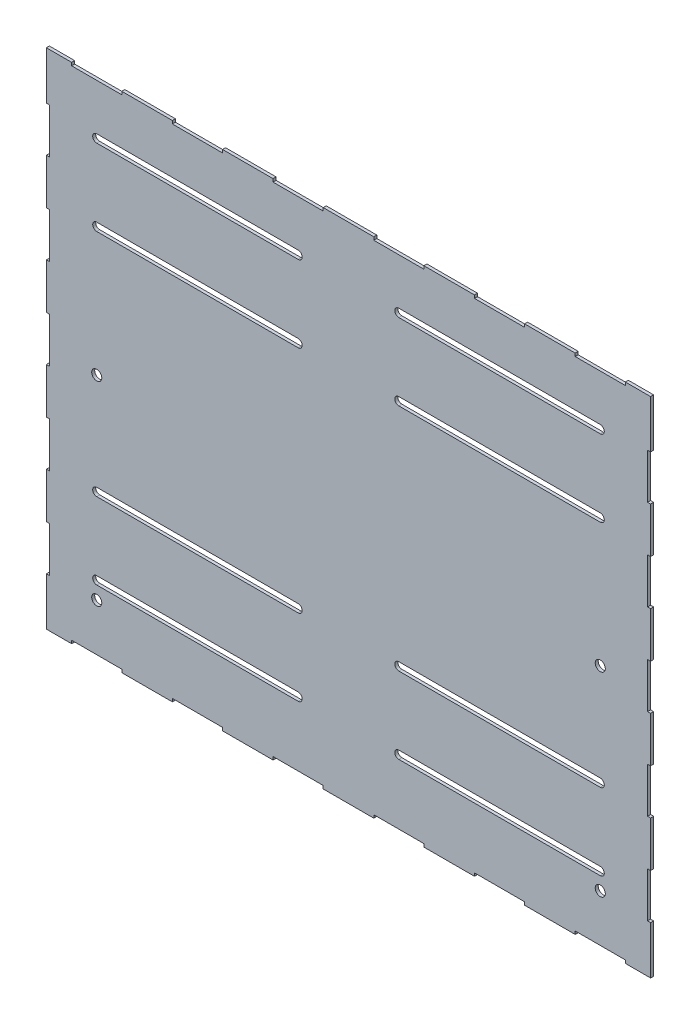
SolidWorks part; units mm, degrees
ref_plane "Alzado" through (0, 0, 0) normal (0, 0, 1) x (1, 0, 0)
ref_plane "Planta" through (0, 0, 0) normal (0, 1, 0) x (1, 0, 0)
ref_plane "Vista lateral" through (0, 0, 0) normal (1, 0, 0) x (0, 0, -1)
sketch "Croquis1" plane through (0, 0, 0) normal (0, 0, 1) x (1, 0, 0)
  line L0 (-250, 197) -> (-50, 197) construction
  line L1 (-300, 250) -> (300, 250)
  line L2 (-300, 250) -> (-300, -250)
  line L3 (-300, -250) -> (300, -250)
  line L4 (300, 250) -> (300, -250)
  line L5 (-300, 250) -> (300, -250) construction
  line L6 (-300, -250) -> (300, 250) construction
  line L7 (-250, 201) -> (-50, 201)
  line L8 (-250, 193) -> (-50, 193)
  line L9 (-250, 117) -> (-50, 117)
  line L10 (-250, 125) -> (-50, 125)
  line L11 (-250, 121) -> (-50, 121) construction
  line L20 (0, 250) -> (0, 163.6039) construction
  line L25 (250, -107) -> (50, -107) construction
  line L26 (-250, -111) -> (-50, -111)
  line L27 (-250, -103) -> (-50, -103)
  line L28 (-250, -107) -> (-50, -107) construction
  line L29 (-250, -187) -> (-50, -187)
  line L30 (-250, -179) -> (-50, -179)
  line L31 (-250, -183) -> (-50, -183) construction
  line L32 (-250, 49) -> (-50, 49) [skipped]
  line L33 (-250, 41) -> (-50, 41) [skipped]
  line L34 (-250, -27) -> (-50, -27) [skipped]
  line L35 (-250, -35) -> (-50, -35) [skipped]
  line L36 (250, -103) -> (50, -103)
  line L37 (250, -111) -> (50, -111)
  line L38 (250, -183) -> (50, -183) construction
  line L39 (250, -179) -> (50, -179)
  line L40 (250, -187) -> (50, -187)
  line L41 (250, 197) -> (50, 197) construction
  line L42 (250, 201) -> (50, 201)
  line L43 (250, 193) -> (50, 193)
  line L44 (250, 121) -> (50, 121) construction
  line L45 (250, 125) -> (50, 125)
  line L46 (250, 117) -> (50, 117)
  line L47 (-241.3, 43.5) -> (241.3, 43.5) construction
  line L48 (0, 0) -> (0, -70.2639) construction
  arc A0 (-250, 201) -> (-250, 193) centre (-250, 197) ccw
  arc A1 (-50, 193) -> (-50, 201) centre (-50, 197) ccw
  arc A10 (-250, 125) -> (-250, 117) centre (-250, 121) ccw
  arc A11 (-50, 117) -> (-50, 125) centre (-50, 121) ccw
  arc A16 (-250, -103) -> (-250, -111) centre (-250, -107) ccw
  arc A17 (-50, -111) -> (-50, -103) centre (-50, -107) ccw
  arc A18 (-250, -179) -> (-250, -187) centre (-250, -183) ccw
  arc A19 (-50, -187) -> (-50, -179) centre (-50, -183) ccw
  arc A20 (-250, 49) -> (-250, 41) centre (-250, 45) ccw [skipped]
  arc A21 (-50, 41) -> (-50, 49) centre (-50, 45) ccw [skipped]
  arc A22 (-250, -27) -> (-250, -35) centre (-250, -31) ccw [skipped]
  arc A23 (-50, -35) -> (-50, -27) centre (-50, -31) ccw [skipped]
  arc A24 (250, -103) -> (250, -111) centre (250, -107) cw
  arc A25 (50, -111) -> (50, -103) centre (50, -107) cw
  arc A26 (250, -179) -> (250, -187) centre (250, -183) cw
  arc A27 (50, -187) -> (50, -179) centre (50, -183) cw
  arc A28 (250, 201) -> (250, 193) centre (250, 197) cw
  arc A29 (50, 193) -> (50, 201) centre (50, 197) cw
  arc A30 (250, 125) -> (250, 117) centre (250, 121) cw
  arc A31 (50, 117) -> (50, 125) centre (50, 121) cw
  circle A32 centre (-250, -200) radius 5
  circle A33 centre (-250, -6.5) radius 5
  circle A34 centre (250, -200) radius 5
  circle A35 centre (250, -6.5) radius 5
  point P0 (0, 0)
  point P8 (-150, 197)
  point P17 (-150, 121)
  point P24 (150, -107)
  point P31 (150, -183)
  point P38 (-150, -107)
  point P45 (-150, -183)
  point P72 (150, 197)
  point P79 (150, 121)
  dimension "D5" = 200
  dimension "D10" = 10
  dimension "D12" = 10
  dimension "D1" = 500
  dimension "D2" = 600
  dimension "D3" = 8
  dimension "D4" = 49
  dimension "D6" = 50
  dimension "D8" = 6
  dimension "D7" = 76
  dimension "D9" = 50
  dimension "D11" = 50
  dimension "D13" = 50
  dimension "D14" = 50
extrude "Saliente-Extruir1" add sketch "Croquis1" along normal blind 3 contours L1 A35 A33 L2 L3 L4 L46 A31 L45 A30 L43 A29 L42 A28 L40 A27 L39 A26 L37 A25 L36 A24 A1 L8 A0 L7 A11 L9 A10 L10 A17 L26 A16 L27 A19 L29 A18 L30 A32
sketch "Croquis5" plane through (0, 0, 0) normal (0, 0, -1) x (-1, 0, 0)
  line L0 (300, 250) -> (-300, 250) construction
  line L1 (300, 250) -> (300, -250) construction
  line L2 (125.1, 250) -> (125.1, 247)
  line L3 (125.1, 247) -> (174.9, 247)
  line L28 (174.9, 247) -> (174.9, 250)
  line L29 (174.9, 250) -> (125.1, 250)
  line L30 (25.1, 250) -> (25.1, 247)
  line L31 (25.1, 247) -> (74.9, 247)
  line L32 (225.1, 250) -> (225.1, 247)
  line L33 (225.1, 247) -> (274.9, 247)
  line L34 (274.9, 247) -> (274.9, 250)
  line L35 (274.9, 250) -> (225.1, 250)
  line L52 (74.9, 247) -> (74.9, 250)
  line L53 (74.9, 250) -> (25.1, 250)
  line L54 (-74.9, 250) -> (-74.9, 247)
  line L55 (-74.9, 247) -> (-25.1, 247)
  line L148 (-25.1, 247) -> (-25.1, 250)
  line L149 (-25.1, 250) -> (-74.9, 250)
  line L150 (-174.9, 250) -> (-174.9, 247)
  line L151 (-174.9, 247) -> (-125.1, 247)
  line L152 (297, 202.4) -> (297, 157.6)
  line L153 (297, 157.6) -> (300, 157.6)
  line L154 (300, 157.6) -> (300, 202.4)
  line L155 (300, 202.4) -> (297, 202.4)
  line L156 (-125.1, 247) -> (-125.1, 250)
  line L157 (-125.1, 250) -> (-174.9, 250)
  line L158 (-274.9, 250) -> (-274.9, 247)
  line L159 (-274.9, 247) -> (-225.1, 247)
  line L160 (-225.1, 247) -> (-225.1, 250)
  line L161 (-225.1, 250) -> (-274.9, 250)
  line L182 (297, 112.4) -> (297, 67.6)
  line L183 (297, 67.6) -> (300, 67.6)
  line L184 (300, 67.6) -> (300, 112.4)
  line L185 (300, 112.4) -> (297, 112.4)
  line L186 (297, 22.4) -> (297, -22.4)
  line L187 (297, -22.4) -> (300, -22.4)
  line L188 (300, -22.4) -> (300, 22.4)
  line L189 (300, 22.4) -> (297, 22.4)
  line L190 (297, -67.6) -> (297, -112.4)
  line L191 (297, -112.4) -> (300, -112.4)
  line L192 (300, -112.4) -> (300, -67.6)
  line L193 (300, -67.6) -> (297, -67.6)
  line L194 (297, -157.6) -> (297, -202.4)
  line L195 (297, -202.4) -> (300, -202.4)
  line L196 (300, -202.4) -> (300, -157.6)
  line L197 (300, -157.6) -> (297, -157.6)
  line L198 (0, 0) -> (0, 89.4251) construction
  line L199 (0, 0) -> (95.335, 0) construction
  line L200 (-225.1, -250) -> (-274.9, -250)
  line L201 (-225.1, -247) -> (-225.1, -250)
  line L202 (-274.9, -247) -> (-225.1, -247)
  line L203 (-274.9, -250) -> (-274.9, -247)
  line L204 (-125.1, -250) -> (-174.9, -250)
  line L205 (-125.1, -247) -> (-125.1, -250)
  line L206 (-174.9, -247) -> (-125.1, -247)
  line L207 (-174.9, -250) -> (-174.9, -247)
  line L208 (-25.1, -250) -> (-74.9, -250)
  line L209 (-25.1, -247) -> (-25.1, -250)
  line L210 (-74.9, -247) -> (-25.1, -247)
  line L211 (-74.9, -250) -> (-74.9, -247)
  line L212 (74.9, -250) -> (25.1, -250)
  line L213 (74.9, -247) -> (74.9, -250)
  line L214 (274.9, -250) -> (225.1, -250)
  line L215 (274.9, -247) -> (274.9, -250)
  line L216 (225.1, -247) -> (274.9, -247)
  line L217 (225.1, -250) -> (225.1, -247)
  line L218 (25.1, -247) -> (74.9, -247)
  line L219 (25.1, -250) -> (25.1, -247)
  line L220 (174.9, -250) -> (125.1, -250)
  line L221 (174.9, -247) -> (174.9, -250)
  line L222 (125.1, -247) -> (174.9, -247)
  line L223 (125.1, -250) -> (125.1, -247)
  line L224 (-300, -157.6) -> (-297, -157.6)
  line L225 (-300, -202.4) -> (-300, -157.6)
  line L226 (-297, -202.4) -> (-300, -202.4)
  line L227 (-297, -157.6) -> (-297, -202.4)
  line L228 (-300, -67.6) -> (-297, -67.6)
  line L229 (-300, -112.4) -> (-300, -67.6)
  line L230 (-297, -112.4) -> (-300, -112.4)
  line L231 (-297, -67.6) -> (-297, -112.4)
  line L232 (-300, 22.4) -> (-297, 22.4)
  line L233 (-300, -22.4) -> (-300, 22.4)
  line L234 (-297, -22.4) -> (-300, -22.4)
  line L235 (-297, 22.4) -> (-297, -22.4)
  line L236 (-300, 112.4) -> (-297, 112.4)
  line L237 (-300, 67.6) -> (-300, 112.4)
  line L238 (-297, 67.6) -> (-300, 67.6)
  line L239 (-297, 112.4) -> (-297, 67.6)
  line L240 (-300, 202.4) -> (-297, 202.4)
  line L241 (-300, 157.6) -> (-300, 202.4)
  line L242 (-297, 157.6) -> (-300, 157.6)
  line L243 (-297, 202.4) -> (-297, 157.6)
  dimension "D1" = 47.6
  dimension "D2" = 44.8
  dimension "D3" = 3
  dimension "D4" = 25.1
  dimension "D5" = 49.8
  dimension "D6" = 3
  dimension "D8" = 50.2
  dimension "D9" = 45.2
  dimension "D7" = 6
  dimension "D10" = 5
extrude "Cortar-Extruir2" cut sketch "Croquis5" against normal through all
